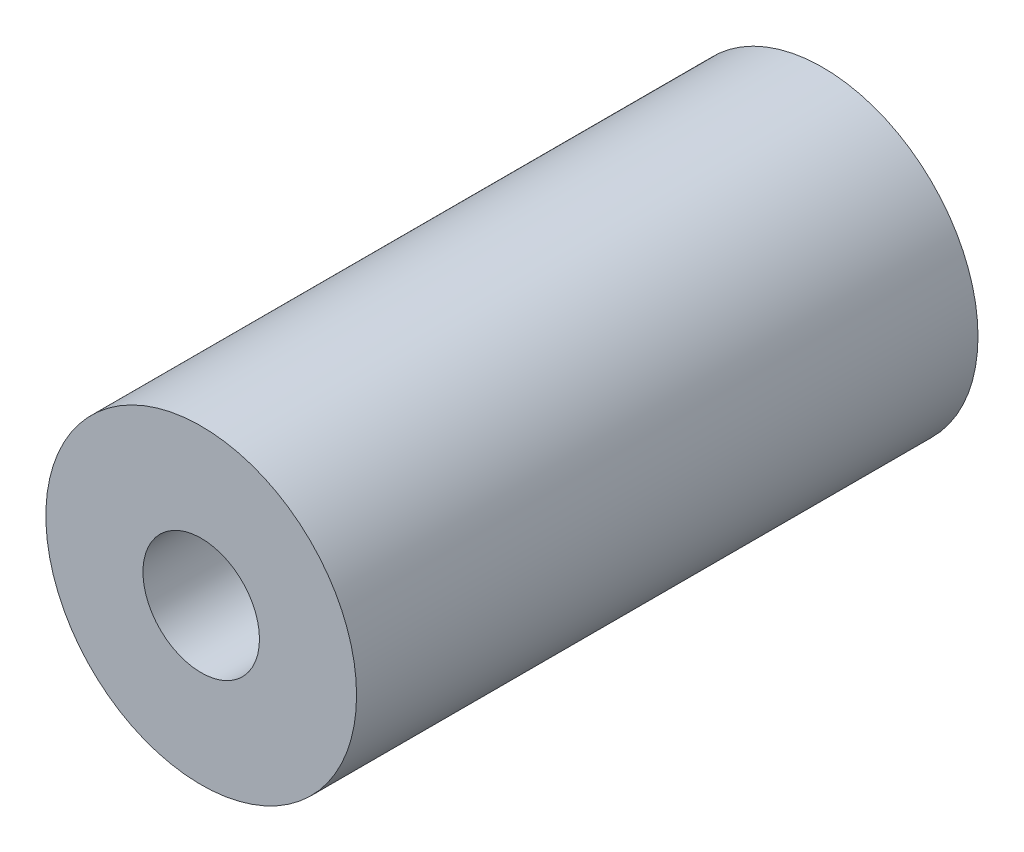
SolidWorks part; units mm, degrees
ref_plane "Plano frontal" through (0, 0, 0) normal (0, 0, 1) x (1, 0, 0)
ref_plane "Plano superior" through (0, 0, 0) normal (0, 1, 0) x (1, 0, 0)
ref_plane "Plano direito" through (0, 0, 0) normal (1, 0, 0) x (0, 0, -1)
sketch "Sketch1" plane through (0, 0, 0) normal (0, 0, 1) x (1, 0, 0)
  circle A0 centre (0, 0) radius 1.5
  circle A1 centre (0, 0) radius 4
extrude "Boss-Extrude1" add sketch "Sketch1" along normal blind 16
